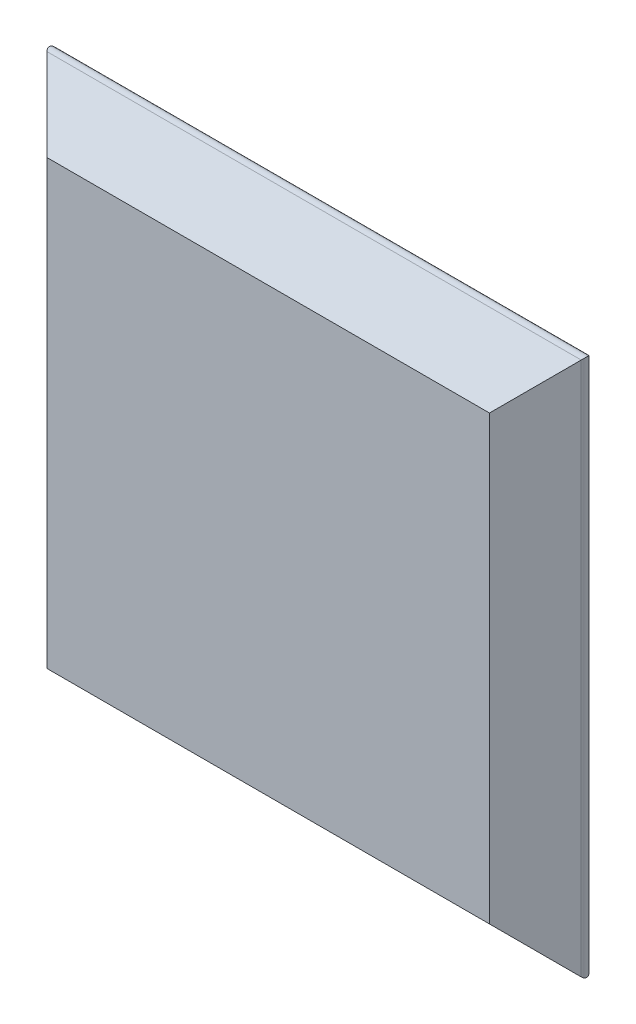
SolidWorks part; units mm, degrees
ref_plane "Front Plane" through (0, 0, 0) normal (0, 0, 1) x (1, 0, 0)
ref_plane "Top Plane" through (0, 0, 0) normal (0, 1, 0) x (1, 0, 0)
ref_plane "Right Plane" through (0, 0, 0) normal (1, 0, 0) x (0, 0, -1)
sketch "Sketch1" plane through (0, 0, 0) normal (0, 0, 1) x (1, 0, 0)
  line L1 (-50, -50) -> (50, -50)
  line L2 (-50, -50) -> (-50, 50)
  line L3 (-50, 50) -> (50, 50)
  line L4 (50, -50) -> (50, 50)
  line L5 (-50, -50) -> (50, 50) construction
  line L6 (-50, 50) -> (50, -50) construction
  point P0 (0, 0)
extrude "Boss-Extrude1" add sketch "Sketch1" along normal blind 10 draft 45
fillet "Fillet1" radius 1 4 edges at (0, 50, 0) (-50, 0, 0) (0, -50, 0) (50, 0, 0)
equation "\"A\"= 100"
equation "\"B\"= 100"
equation "\"C\" = 10"
equation "\"D1@Sketch1\"=\"A\""
equation "\"D2@Sketch1\"=\"B\""
equation "\"D1@Boss-Extrude1\"=\"C\""
equation "\"Holes Frame\"= \"A\" - ( \"A\" * ( 3 / 10 ) )"
equation "\"LED Ø\"= 10"
